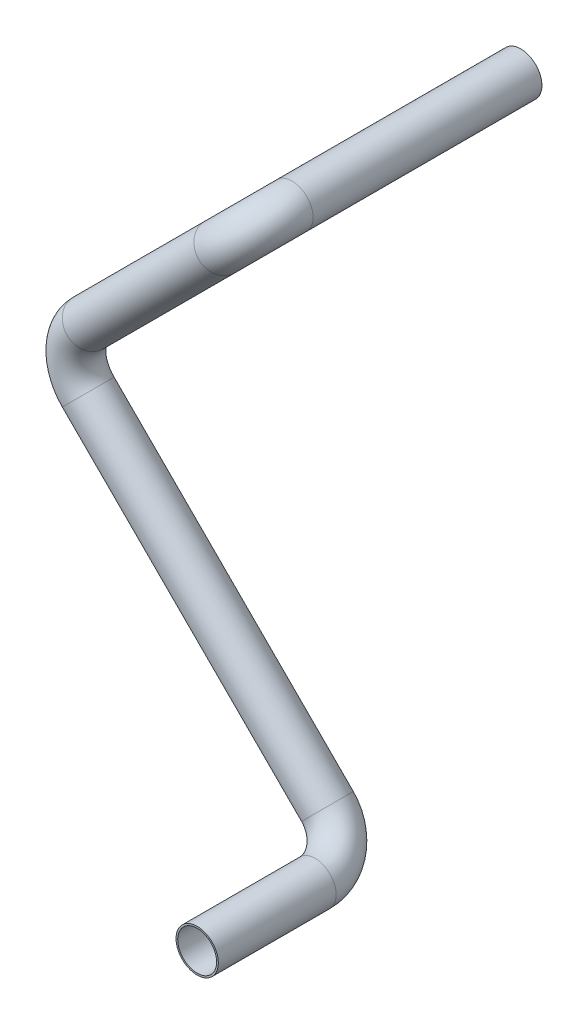
SolidWorks part; units mm, degrees
ref_plane "Front" through (0, 0, 0) normal (0, 0, 1) x (1, 0, 0)
ref_plane "Top" through (0, 0, 0) normal (0, 1, 0) x (1, 0, 0)
ref_plane "Side" through (0, 0, 0) normal (1, 0, 0) x (0, 0, -1)
sketch "PipeSketch" plane through (0, 0, 0) normal (0, 0, 1) x (1, 0, 0)
  circle A0 centre (0, 0) radius 6.35
  circle A1 centre (0, 0) radius 5.842 construction
  dimension "OuterDiameter" = 12.7
  dimension "InnerDiameter" = 11.684
sketch "FilterSketch" plane through (0, 0, 0) normal (0, 0, 1) x (1, 0, 0)
  circle A0 centre (0, 0) radius 6.35 construction
  dimension "NominalDiameter" = 12.7
sketch3d "3DSketch1"
  line L0 (0, 0, 10) -> (0, 0, 68.7121) construction
  line L1 (-8.9803, -8.9803, 81.4121) -> (-48.4934, -48.4934, 81.4121) construction
  line L2 (-48.4934, -66.4539, 81.4121) -> (23.3487, -138.2959, 81.4121) construction
  line L3 (32.3289, -147.2762, 119.5121) -> (32.3289, -147.2762, 94.1121) construction
  line L4 (0, 0, 0) -> (0, 0, 68.7121)
  line L5 (-8.9803, -8.9803, 81.4121) -> (-48.4934, -48.4934, 81.4121)
  line L6 (-48.4934, -66.4539, 81.4121) -> (23.3487, -138.2959, 81.4121)
  line L7 (32.3289, -147.2762, 129.5121) -> (32.3289, -147.2762, 94.1121)
  arc A0 (0, 0, 68.7121) -> (-8.9803, -8.9803, 81.4121) centre (-8.9803, -8.9803, 68.7121) ccw construction
  arc A1 (-48.4934, -48.4934, 81.4121) -> (-48.4934, -66.4539, 81.4121) centre (-39.5131, -57.4736, 81.4121) ccw construction
  arc A2 (23.3487, -138.2959, 81.4121) -> (32.3289, -147.2762, 94.1121) centre (23.3487, -138.2959, 94.1121) ccw construction
  arc A3 (0, 0, 68.7121) -> (-8.9803, -8.9803, 81.4121) centre (-8.9803, -8.9803, 68.7121) ccw
  arc A4 (-48.4934, -48.4934, 81.4121) -> (-48.4934, -66.4539, 81.4121) centre (-39.5131, -57.4736, 81.4121) ccw
  arc A5 (23.3487, -138.2959, 81.4121) -> (32.3289, -147.2762, 94.1121) centre (23.3487, -138.2959, 94.1121) ccw
  point P4 (0, -17.9605, 68.7121)
  point P6 (0, -17.9605, 68.7121)
  point P7 (-39.5131, -57.4736, 94.1121)
  point P10 (14.3684, -147.2762, 94.1121)
  point P12 (-39.5131, -57.4736, 94.1121)
  point P18 (14.3684, -147.2762, 94.1121)
sweep "ThinSweep" add profiles "PipeSketch" path "3DSketch1" parameters "WallThickness"=0.508
ref_plane "Plane1" through (0, 0, 0) normal (0, 0, 1) x (1, 0, 0)
sketch3d "PATH"
  line L0 (0, 0, 0) -> (0, 0, 81.4121)
  line L1 (0, 0, 81.4121) -> (-57.4736, -57.4736, 81.4121)
  line L2 (-57.4736, -57.4736, 81.4121) -> (32.3289, -147.2762, 81.4121)
  line L3 (32.3289, -147.2762, 81.4121) -> (32.3289, -147.2762, 129.5121)
  line L4 (32.3289, -147.2762, 129.5121) -> (32.3289, -147.2762, 94.1121) construction
  line L5 (-48.4934, -66.4539, 81.4121) -> (23.3487, -138.2959, 81.4121) construction
  line L6 (-8.9803, -8.9803, 81.4121) -> (-48.4934, -48.4934, 81.4121) construction
  line L7 (0, 0, 0) -> (0, 0, 68.7121) construction
